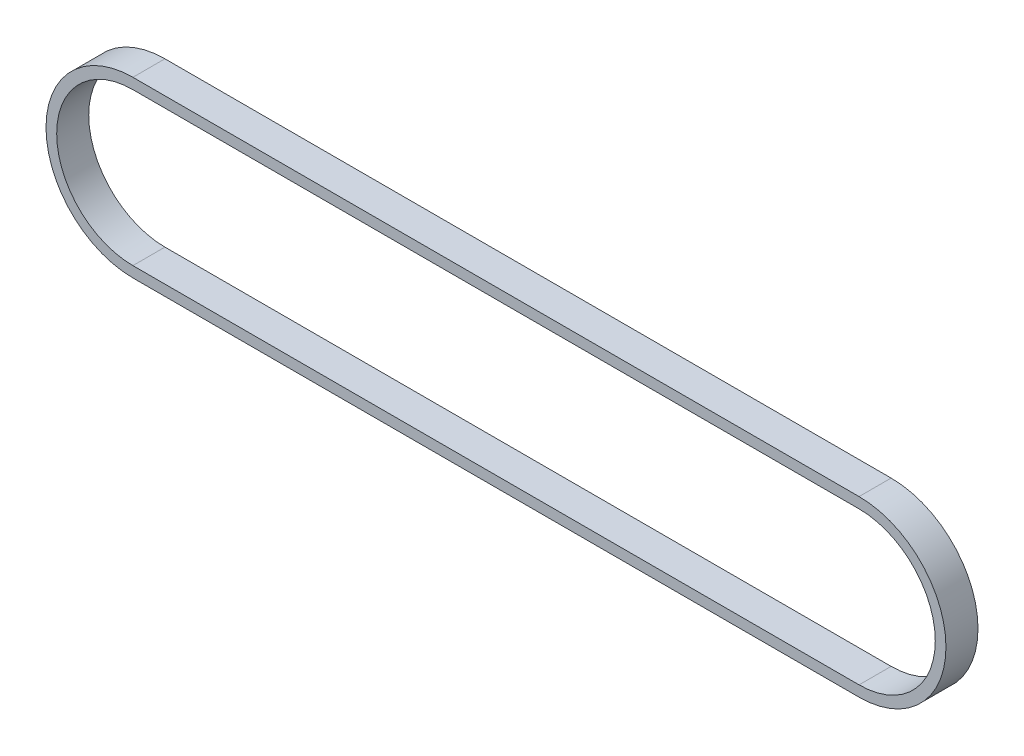
SolidWorks part; units mm, degrees
material "NEOPRENE"
ref_plane "Plano frontal" through (0, 0, 0) normal (0, 0, 1) x (1, 0, 0)
ref_plane "Plano superior" through (0, 0, 0) normal (0, 1, 0) x (1, 0, 0)
ref_plane "Plano direito" through (0, 0, 0) normal (1, 0, 0) x (0, 0, -1)
sketch "Esboço1" plane through (0, 0, 0) normal (0, 0, 1) x (1, 0, 0)
  line L0 (0, 22.9) -> (203.9448, 22.9) construction
  line L1 (0, -22.9) -> (203.9448, -22.9) construction
  line L2 (0, 21.4) -> (203.9448, 21.4)
  line L3 (0, -24.4) -> (203.9448, -24.4)
  line L4 (0, 24.4) -> (203.9448, 24.4)
  line L5 (0, -21.4) -> (203.9448, -21.4)
  circle A0 centre (0, 0) radius 22.9 construction
  circle A1 centre (203.9448, 0) radius 22.9 construction
  circle A2 centre (0, 0) radius 24.4
  circle A3 centre (203.9448, 0) radius 24.4
  circle A4 centre (0, 0) radius 21.4
  circle A5 centre (203.9448, 0) radius 21.4
  dimension "D1" = 45.8
  dimension "D2" = 203.9448
  dimension "D3" = 1.5
  dimension "D4" = 1.5
extrude "Ressalto-extrusão1" add sketch "Esboço1" along normal mid plane 9 contours A4 L2 A2 L5 | A3 L4 A2 L2 | A3 L5 A2 L3 | A5 L5 A3 L2
